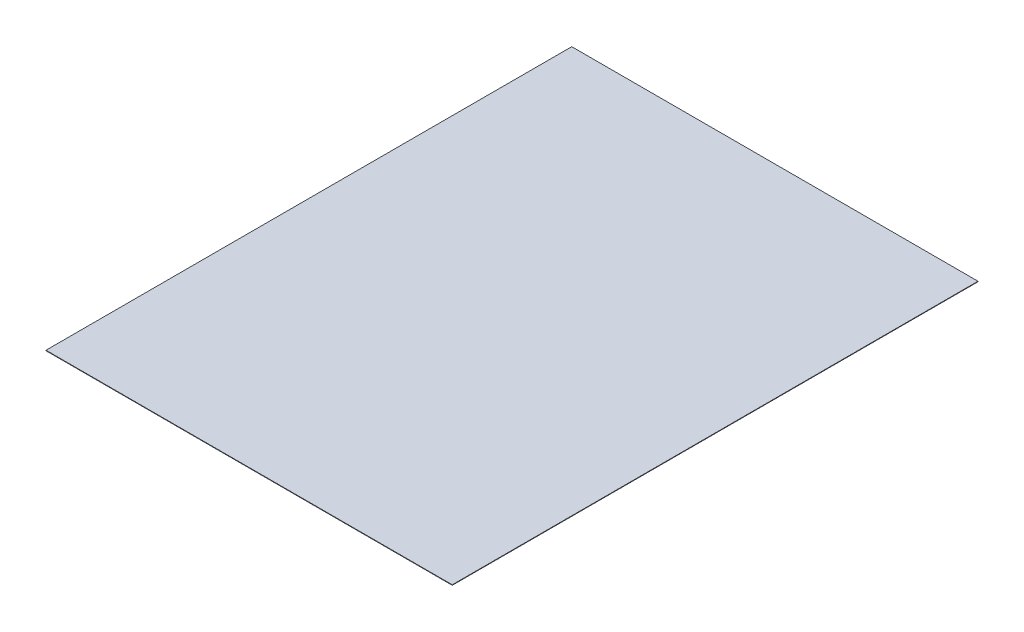
SolidWorks part; units mm, degrees
material "Teak"
ref_plane "Front Plane" through (0, 0, 0) normal (0, 0, 1) x (1, 0, 0)
ref_plane "Top Plane" through (0, 0, 0) normal (0, 1, 0) x (1, 0, 0)
ref_plane "Right Plane" through (0, 0, 0) normal (1, 0, 0) x (0, 0, -1)
sketch "Sketch1" plane through (0, 0, 0) normal (0, 1, 0) x (1, 0, 0)
  line L1 (0, 0) -> (215.9, 0)
  line L2 (0, 0) -> (0, 279.4)
  line L3 (0, 279.4) -> (215.9, 279.4)
  line L4 (215.9, 0) -> (215.9, 279.4)
  dimension "D1" = 215.9
  dimension "D2" = 279.4
extrude "Boss-Extrude1" add sketch "Sketch1" along normal blind 0.254
